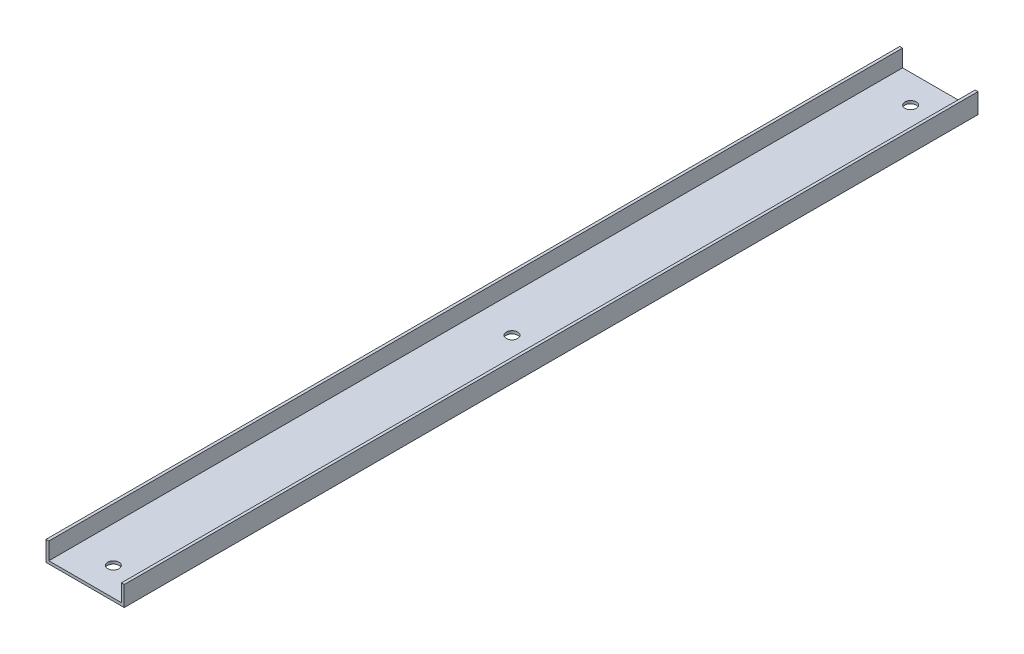
SolidWorks part; units mm, degrees
ref_plane "Front Plane" through (0, 0, 0) normal (0, 0, 1) x (1, 0, 0)
ref_plane "Top Plane" through (0, 0, 0) normal (0, 1, 0) x (1, 0, 0)
ref_plane "Right Plane" through (0, 0, 0) normal (1, 0, 0) x (0, 0, -1)
sketch "Sketch1" plane through (0, 0, 0) normal (0, 0, 1) x (1, 0, 0)
  line L0 (0, 0) -> (0, -8.9916)
  line L1 (0, -8.9916) -> (35.2044, -8.9916)
  line L2 (35.2044, -8.9916) -> (35.2044, 0)
  line L3 (35.2044, 0) -> (33.9344, 0)
  line L4 (33.9344, 0) -> (33.9344, -7.7216)
  line L5 (33.9344, -7.7216) -> (1.27, -7.7216)
  line L6 (1.27, -7.7216) -> (1.27, 0)
  line L7 (1.27, 0) -> (0, 0)
  dimension "D1" = 35.2044
  dimension "D2" = 8.9916
  dimension "D3" = 1.27
  dimension "D4" = 1.27
  dimension "D5" = 1.27
extrude "Boss-Extrude1" add sketch "Sketch1" along normal blind 384.175
sketch "Sketch2" plane through (0, -8.9916, 0) normal (0, -1, 0) x (-1, 0, 0)
  line L0 (-17.6022, 0) -> (-17.6022, -384.175) construction
  line L1 (0, 0) -> (-35.2044, 0) construction
  line L2 (0, -384.175) -> (-35.2044, -384.175) construction
  circle A0 centre (-17.6022, -12.7) radius 2.54
  circle A1 centre (-17.6022, -192.0875) radius 2.54
  circle A2 centre (-17.6022, -371.475) radius 2.54
  dimension "D1" = 5.08
  dimension "D2" = 12.7
  dimension "D4" = 12.7
extrude "Cut-Extrude1" cut sketch "Sketch2" against normal blind 1.27
ref_plane "Center plane" through (17.6022, 0, 0) normal (1, 0, 0) x (0, 0, -1)
